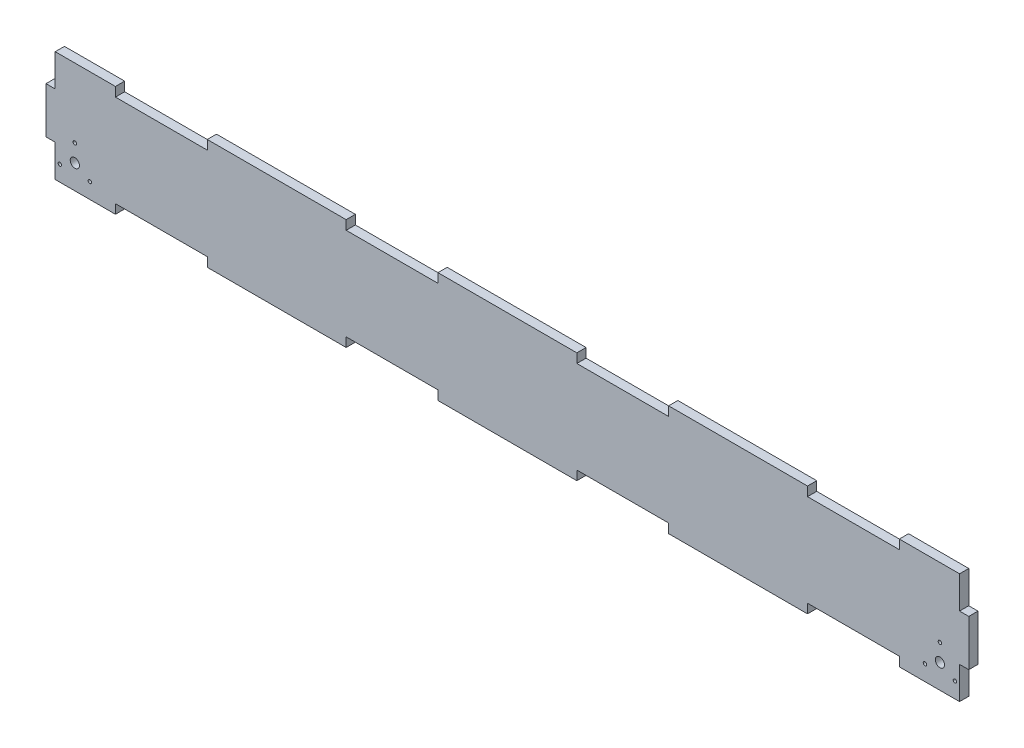
SolidWorks part; units mm, degrees
ref_plane "Front Plane" through (0, 0, 0) normal (0, 0, 1) x (1, 0, 0)
ref_plane "Top Plane" through (0, 0, 0) normal (0, 1, 0) x (1, 0, 0)
ref_plane "Right Plane" through (0, 0, 0) normal (1, 0, 0) x (0, 0, -1)
sketch "Sketch1" plane through (0, 0, 0) normal (0, 0, 1) x (1, 0, 0)
  line L0 (392, -20) -> (392, -48)
  line L1 (392, -48) -> (339.8, -48)
  line L2 (-400, 19.8) -> (-400, 20)
  line L3 (392, 48) -> (339.8, 48)
  line L5 (400, -48) -> (-400, 48) construction
  line L6 (400, 48) -> (-400, -48) construction
  line L7 (339.8, 40) -> (260.2, 40)
  line L9 (339.8, -40) -> (260.2, -40)
  line L10 (0, 0) -> (0, 150.7246) construction
  line L11 (-200, 171.805) -> (-200, -11.5942) construction
  line L12 (-300, 150.7246) -> (-300, -11.5942) construction
  line L13 (-339.8, 48) -> (-339.8, 40)
  line L14 (-260.2, 48) -> (-260.2, 40)
  line L15 (-139.8, 48) -> (-139.8, 40)
  line L16 (-60.2, 48) -> (-60.2, 40)
  line L17 (60.2, 48) -> (60.2, 40)
  line L18 (139.8, 48) -> (139.8, 40)
  line L19 (260.2, 48) -> (260.2, 40)
  line L20 (339.8, 48) -> (339.8, 40)
  line L21 (0, 0) -> (-499.1198, 0) construction
  line L23 (-400, -20) -> (-392, -20)
  line L24 (392, 20) -> (400, 20)
  line L25 (392, -20) -> (400, -20)
  line L26 (339.8, -48) -> (339.8, -40)
  line L27 (260.2, -48) -> (260.2, -40)
  line L28 (139.8, -48) -> (139.8, -40)
  line L29 (60.2, -48) -> (60.2, -40)
  line L30 (-60.2, -48) -> (-60.2, -40)
  line L31 (-139.8, -48) -> (-139.8, -40)
  line L32 (-260.2, -48) -> (-260.2, -40)
  line L33 (-339.8, -48) -> (-339.8, -40)
  line L34 (-339.8, 48) -> (-392, 48)
  line L35 (-260.2, 40) -> (-339.8, 40)
  line L36 (400, 48) -> (-400, 48) construction
  line L37 (392, 40) -> (-392, 40) construction
  line L38 (-392, -40) -> (-392, 40) construction
  line L39 (-60.2, 40) -> (-139.8, 40)
  line L40 (-139.8, 48) -> (-260.2, 48)
  line L41 (60.2, 48) -> (-60.2, 48)
  line L42 (139.8, 40) -> (60.2, 40)
  line L43 (260.2, 48) -> (139.8, 48)
  line L44 (400, 19.8) -> (400, 20)
  line L45 (392, -40) -> (392, 40) construction
  line L46 (260.2, -48) -> (139.8, -48)
  line L47 (400, -48) -> (400, 48) construction
  line L48 (392, -40) -> (-392, -40) construction
  line L49 (139.8, -40) -> (60.2, -40)
  line L50 (400, -48) -> (-400, -48) construction
  line L51 (60.2, -48) -> (-60.2, -48)
  line L52 (-60.2, -40) -> (-139.8, -40)
  line L53 (-139.8, -48) -> (-260.2, -48)
  line L54 (-260.2, -40) -> (-339.8, -40)
  line L55 (-339.8, -48) -> (-392, -48)
  line L57 (-400, 19.8) -> (-400, -20)
  line L58 (-400, -48) -> (-400, 48) construction
  line L59 (400, 19.8) -> (400, -20)
  line L60 (-400, 20) -> (-392, 20)
  line L62 (-392, 20) -> (-392, 48)
  line L63 (-392, -20) -> (-392, -48)
  line L64 (392, 20) -> (392, 48)
  point P0 (0, 0)
  point P18 (-339.8, 44)
  dimension "D1" = 800
  dimension "D2" = 96
  dimension "D4" = 200
  dimension "D5" = 100
  dimension "D6" = 39.8
  dimension "D7" = 20
  dimension "D8" = 20
  dimension "D3" = 8
extrude "Boss-Extrude1" add sketch "Sketch1" along normal blind 8
sketch "Sketch2" plane through (0, 0, 8) normal (0, 0, 1) x (1, 0, 0)
  line L0 (-339.8, 48) -> (-392, 48) construction
  line L1 (-400, 20) -> (-400, -20) construction
  line L2 (0, 0) -> (0, 125.7976) construction
  line L3 (-375, -27) -> (-375, 10.1703) construction
  circle A0 centre (-375, -27) radius 4
  circle A1 centre (375, -27) radius 4
  circle A2 centre (-375, -12) radius 1.5
  circle A3 centre (-375, -12) radius 1.5
  circle A4 centre (-375, -12) radius 1.5
  circle A5 centre (375, -12) radius 1.5
  circle A6 centre (375, -12) radius 1.5
  circle A7 centre (375, -12) radius 1.5
  circle A8 centre (375, -27) radius 4
  circle A9 centre (-362.0096, -34.5) radius 1.5
  circle A10 centre (-387.9904, -34.5) radius 1.5
  circle A11 centre (387.9904, -34.5) radius 1.5
  circle A12 centre (362.0096, -34.5) radius 1.5
  point P20 (-375, -12)
  point P32 (-375, -27)
  dimension "D3" = 8
  dimension "D4" = 3
  dimension "D1" = 75
  dimension "D2" = 25
  dimension "D5" = 15
  dimension "D6" = 3
  dimension "D7" = 3
extrude "Cut-Extrude1" cut sketch "Sketch2" against normal blind 10 contours A4 | A3 | A0 | A2 | A7 | A6 | A1 | A5 | A10 | A9 | A12 | A11
